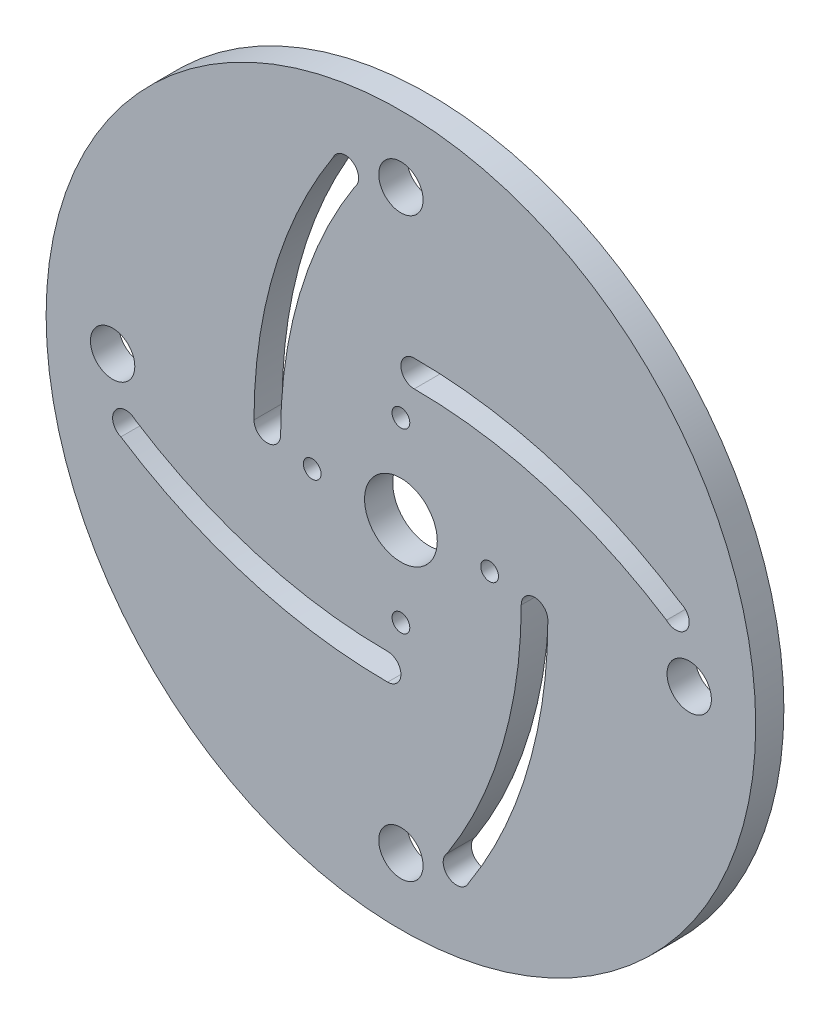
SolidWorks part; units mm, degrees
ref_plane "Front Plane" through (0, 0, 0) normal (0, 0, 1) x (1, 0, 0)
ref_plane "Top Plane" through (0, 0, 0) normal (0, 1, 0) x (1, 0, 0)
ref_plane "Right Plane" through (0, 0, 0) normal (1, 0, 0) x (0, 0, -1)
sketch "Sketch1" plane through (0, 0, 0) normal (0, 0, 1) x (1, 0, 0)
  circle A13 centre (0, 0) radius 40
  circle A14 centre (0, 0) radius 4.1
  circle A15 centre (10, 0) radius 1
  circle A16 centre (0, -10) radius 1
  circle A17 centre (-10, 0) radius 1
  circle A18 centre (0, 10) radius 1
  circle A19 centre (0, 32.5) radius 2.5
  circle A20 centre (32.5, 0) radius 2.5
  circle A21 centre (0, -32.5) radius 2.5
  circle A22 centre (-32.5, 0) radius 2.5
  arc A25 (1.5, 16.564) -> (31.574, 7.6531) centre (1.5, -38.6406) cw
  arc A26 (1.5, 13.564) -> (29.9393, 5.2066) centre (1.5, -39.0025) cw
  arc A27 (29.9393, 5.2066) -> (31.574, 7.6531) centre (31, 6.2672) ccw
  arc A28 (1.5, 16.564) -> (1.5, 13.564) centre (1.5, 15.064) ccw
  arc A29 (16.564, -1.5) -> (7.6531, -31.574) centre (-38.6406, -1.5) cw
  arc A30 (5.2066, -29.9393) -> (7.6531, -31.574) centre (6.2672, -31) ccw
  arc A31 (13.564, -1.5) -> (5.2066, -29.9393) centre (-39.0025, -1.5) cw
  arc A32 (16.564, -1.5) -> (13.564, -1.5) centre (15.064, -1.5) ccw
  arc A33 (-1.5, -16.564) -> (-31.574, -7.6531) centre (-1.5, 38.6406) cw
  arc A34 (-29.9393, -5.2066) -> (-31.574, -7.6531) centre (-31, -6.2672) ccw
  arc A35 (-1.5, -13.564) -> (-29.9393, -5.2066) centre (-1.5, 39.0025) cw
  arc A36 (-1.5, -16.564) -> (-1.5, -13.564) centre (-1.5, -15.064) ccw
  arc A37 (-16.564, 1.5) -> (-7.6531, 31.574) centre (38.6406, 1.5) cw
  arc A38 (-5.2066, 29.9393) -> (-7.6531, 31.574) centre (-6.2672, 31) ccw
  arc A39 (-13.564, 1.5) -> (-5.2066, 29.9393) centre (39.0025, 1.5) cw
  arc A40 (-16.564, 1.5) -> (-13.564, 1.5) centre (-15.064, 1.5) ccw
  dimension "D1" = 10
  dimension "D2" = 32.5
  dimension "D3" = 4
extrude "Boss-Extrude1" add sketch "Sketch1" along normal blind 3.175 contours A13
sketch "Sketch2" plane through (0, 0, 3.175) normal (0, 0, 1) x (1, 0, 0)
  arc A0 (-15.0308, 1.5) -> (-6.2672, 31) centre (39.0025, 1.5) cw
  arc A1 (-5.2066, 29.9393) -> (-13.564, 1.5) centre (39.0025, 1.5) ccw construction
  point P6 (-6.2672, 31)
  point P8 (-15.0308, 1.5)
equation "\"D\"= 6in"
